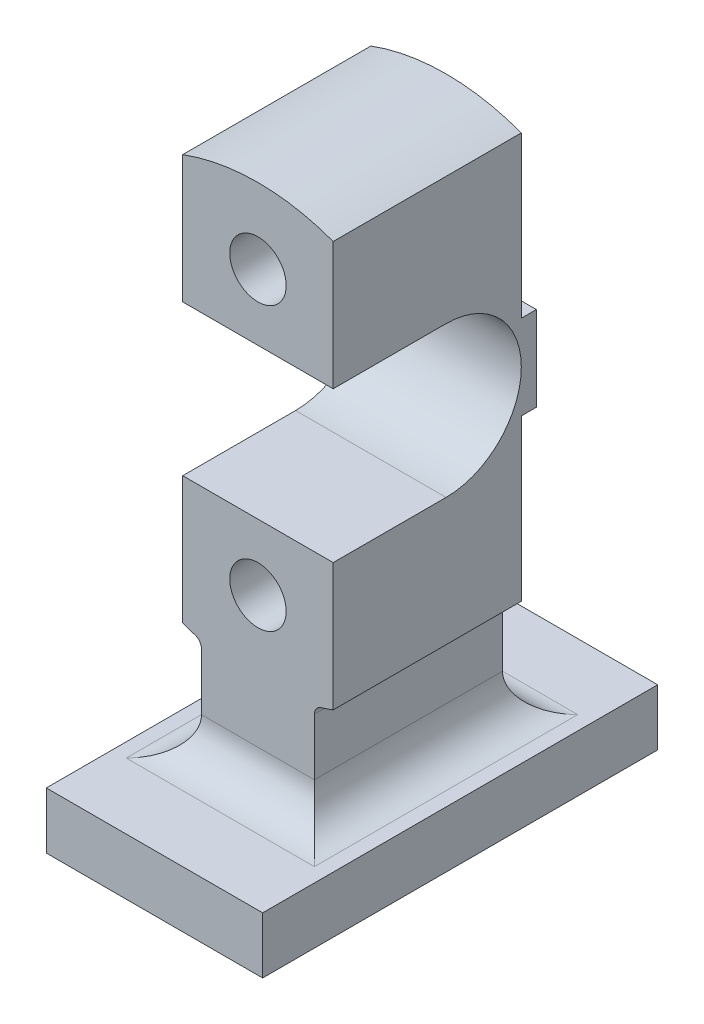
SolidWorks part; units mm, degrees
ref_plane "Front Plane" through (0, 0, 0) normal (0, 0, 1) x (1, 0, 0)
ref_plane "Top Plane" through (0, 0, 0) normal (0, 1, 0) x (1, 0, 0)
ref_plane "Right Plane" through (0, 0, 0) normal (1, 0, 0) x (0, 0, -1)
sketch "Sketch1" plane through (0, 0, 0) normal (0, 0, 1) x (1, 0, 0)
  line L0 (-110.1642, 0) -> (110.1642, 0) construction
  line L2 (40, -107.8193) -> (40, 107.8193)
  line L4 (-40, -107.8193) -> (-40, 107.8193)
  line L5 (40, -107.8193) -> (-40, 107.8193) construction
  line L6 (40, 107.8193) -> (-40, -107.8193) construction
  line L7 (-115.0355, 75) -> (115.0355, 75) construction
  line L8 (-115.0355, -75) -> (115.0355, -75) construction
  line L9 (0, 129.5579) -> (0, -180) construction
  line L10 (-30, -114.7824) -> (-30, -145)
  line L11 (30, -114.7824) -> (30, -145)
  line L12 (-30, -165) -> (30, -165)
  line L14 (-50, -165) -> (63.599, -165)
  arc A0 (-40, -107.8193) -> (-33.5417, -109.9998) centre (0, 0) ccw
  arc A1 (40, 107.8193) -> (-40, 107.8193) centre (0, 0) ccw
  circle A2 centre (0, 75) radius 15
  circle A3 centre (0, -75) radius 15
  arc A4 (-33.5417, -109.9998) -> (-30, -114.7824) centre (-35, -114.7824) cw
  arc A5 (33.5417, -109.9998) -> (30, -114.7824) centre (35, -114.7824) ccw
  arc A6 (33.5417, -109.9998) -> (40, -107.8193) centre (0, 0) ccw
  arc A7 (-50, -165) -> (-30, -145) centre (-50, -145) ccw
  arc A8 (50, -165) -> (30, -145) centre (50, -145) cw
  point P14 (0, 75)
  point P15 (0, -75)
  point P16 (0, 0)
  point P25 (0, -180)
  dimension "D1" = 230
  dimension "D5" = 30
  dimension "D11" = 5
  dimension "D7" = 90
  dimension "D8" = 20
  dimension "D2" = 80
  dimension "D3" = 150
  dimension "D4" = 75
  dimension "D6" = 60
extrude "Boss-Extrude2" add sketch "Sketch1" along normal blind 100 contours L14 A8 L11 A5 A6 L2 A1 L4 A0 A4 L10 A7 L12 A3 A2
sketch "Sketch3" plane through (0, 0, 0) normal (0, 0, 1) x (1, 0, 0)
  line L0 (-50, -165) -> (50, -165) construction
  line L1 (57.5, -195) -> (-57.5, -195)
  line L2 (57.5, -195) -> (57.5, -165)
  line L3 (57.5, -165) -> (-57.5, -165)
  line L4 (-57.5, -195) -> (-57.5, -165)
  line L5 (57.5, -195) -> (-57.5, -165) construction
  line L6 (57.5, -165) -> (-57.5, -195) construction
  line L7 (0, 136.1674) -> (0, -305.5426) construction
  arc A0 (30, -145) -> (50, -165) centre (50, -145) ccw construction
  arc A1 (-50, -165) -> (-30, -145) centre (-50, -145) ccw construction
  point P0 (0, -180)
  dimension "D1" = 115
  dimension "D2" = 30
extrude "Boss-Extrude3" add sketch "Sketch3" along normal mid plane 320
sketch "Sketch4" plane through (57.5, 0, 0) normal (1, 0, 0) x (0, 0, -1)
  line L0 (-160, -195) -> (160, -195) construction
  line L1 (-155, -195) -> (55, -195)
  line L2 (-155, -195) -> (-155, -165)
  line L3 (-155, -165) -> (55, -165)
  line L4 (55, -195) -> (55, -165)
  line L5 (-160, -165) -> (160, -165) construction
  line L6 (-50, 131.4163) -> (-50, -257.1283) construction
  line L7 (-100, -107.8193) -> (-100, 107.8193) construction
  line L8 (0, -107.8193) -> (0, 107.8193) construction
  line L10 (-160, -195) -> (-155, -195)
  line L11 (-160, -195) -> (-160, -165)
  line L12 (-160, -165) -> (-155, -165)
  line L13 (-155, -195) -> (-155, -165)
  line L14 (55, -195) -> (160, -195)
  line L15 (55, -195) -> (55, -165)
  line L16 (55, -165) -> (160, -165)
  line L17 (160, -195) -> (160, -165)
  line M7 (160, -165) -> (-160, -165)
  line M8 (-160, -165) -> (-160, -195)
  line M9 (-160, -195) -> (160, -195)
  dimension "D1" = 210
extrude "Cut-Extrude1" cut sketch "Sketch4" against normal blind 320 contours L2 M9 M7 M8 | L15 L14 L17 L16
fillet "Fillet5" radius 20 1 edges at (0, -165, 100)
fillet "Fillet6" radius 20 1 edges at (0, -165, 0)
sketch "Sketch6" plane through (40, 0, 0) normal (1, 0, 0) x (0, 0, -1)
  line L0 (-236.0186, 0) -> (95.5079, 0) construction
  line L1 (0, -107.8193) -> (0, 107.8193) construction
  line L2 (0, -22.5) -> (8, -22.5)
  line L3 (0, -22.5) -> (0, 22.5)
  line L4 (0, 22.5) -> (8, 22.5)
  line L5 (8, -22.5) -> (8, 22.5)
  dimension "D1" = 45
  dimension "D2" = 8
extrude "Boss-Extrude4" add sketch "Sketch6" against normal blind 80
sketch "Sketch7" plane through (40, 0, 0) normal (1, 0, 0) x (0, 0, -1)
  line L0 (-40, 258.2221) -> (-40, -258.2221) construction
  line L1 (-179.2904, 0) -> (99.2904, 0) construction
  line L2 (0, 22.5) -> (0, 107.8193) construction
  line L3 (-40, 40) -> (-100, 40)
  line L4 (-100, -107.8193) -> (-100, 107.8193) construction
  line L5 (-100, 40) -> (-100, -40)
  line L6 (-100, -40) -> (-40, -40)
  arc A0 (-40, -40) -> (-40, 40) centre (-40, 0) ccw
  point P7 (-40, 0)
  point P8 (-40, 0)
  dimension "D2" = 80
  dimension "D1" = 40
extrude "Cut-Extrude2" cut sketch "Sketch7" against normal blind 80
